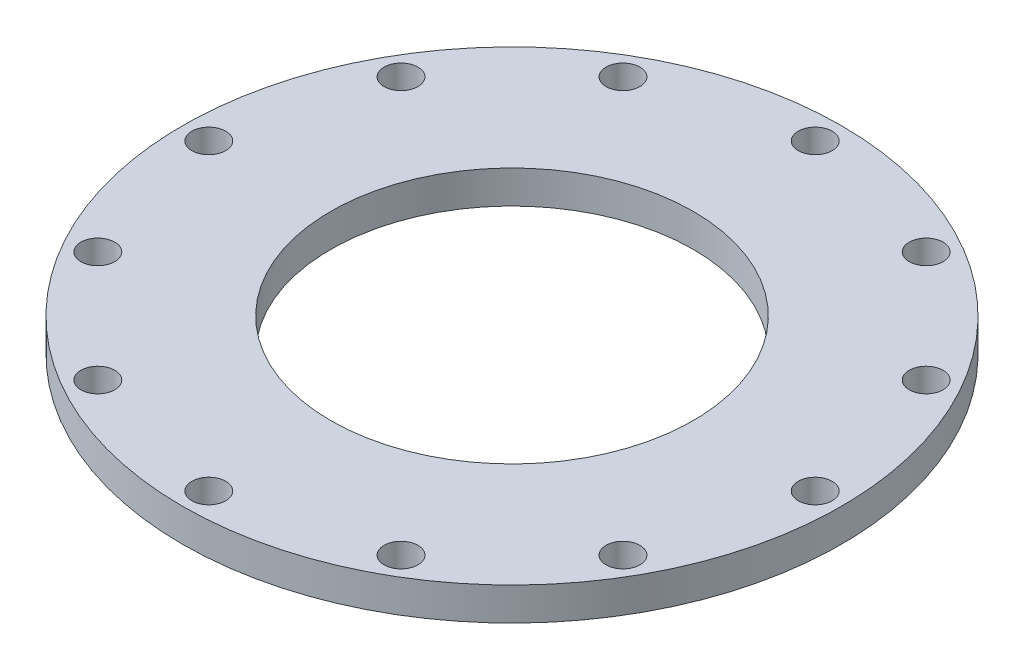
SolidWorks part; units mm, degrees
material "AISI 304"
ref_plane "Front Plane" through (0, 0, 0) normal (0, 0, 1) x (1, 0, 0)
ref_plane "Top Plane" through (0, 0, 0) normal (0, 1, 0) x (1, 0, 0)
ref_plane "Right Plane" through (0, 0, 0) normal (1, 0, 0) x (0, 0, -1)
sketch "Sketch1" plane through (0, 0, 0) normal (0, 1, 0) x (1, 0, 0)
  circle A0 centre (0, 0) radius 63.5
  circle A1 centre (0, 0) radius 34.925
  circle A2 centre (0, 0) radius 58.42 construction
  circle A3 centre (0, 58.42) radius 3.2639
  circle A4 centre (29.21, 50.5932) radius 3.2639
  circle A5 centre (50.5932, 29.21) radius 3.2639
  circle A6 centre (58.42, 0) radius 3.2639
  circle A7 centre (50.5932, -29.21) radius 3.2639
  circle A8 centre (29.21, -50.5932) radius 3.2639
  circle A9 centre (0, -58.42) radius 3.2639
  circle A10 centre (-29.21, -50.5932) radius 3.2639
  circle A11 centre (-50.5932, -29.21) radius 3.2639
  circle A12 centre (-58.42, 0) radius 3.2639
  circle A13 centre (-50.5932, 29.21) radius 3.2639
  circle A14 centre (-29.21, 50.5932) radius 3.2639
  point P32 (0, 0)
  dimension "D1" = 127
  dimension "D2" = 69.85
  dimension "D3" = 116.84
  dimension "D4" = 6.5278
  dimension "D5" = 12
extrude "Boss-Extrude1" add sketch "Sketch1" along normal blind 6.35
